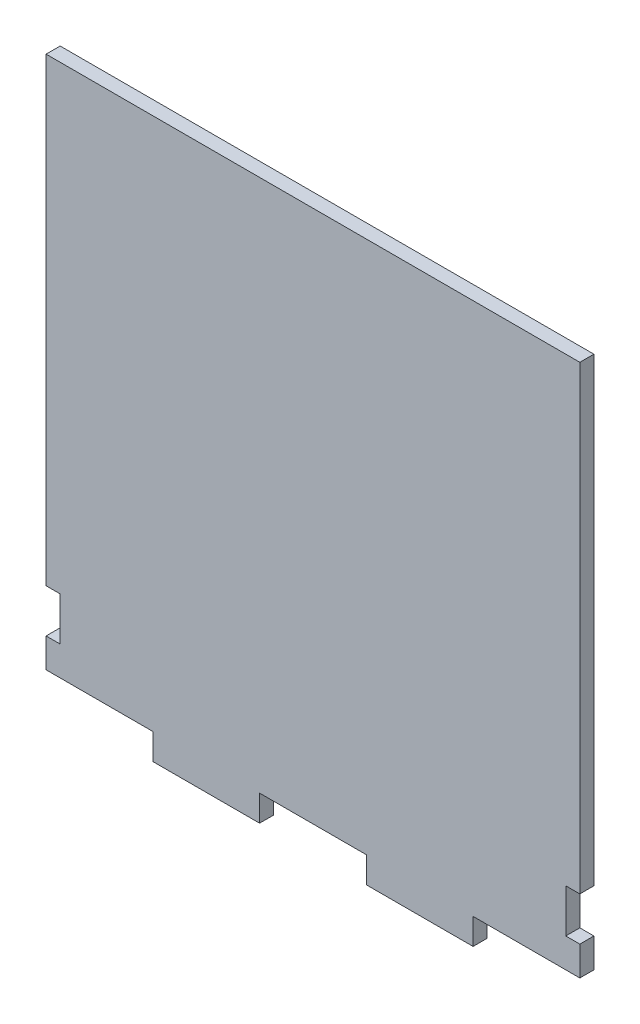
SolidWorks part; units mm, degrees
ref_plane "Ön Düzlem" through (0, 0, 0) normal (0, 0, 1) x (1, 0, 0)
ref_plane "Üst Düzlem" through (0, 0, 0) normal (0, 1, 0) x (1, 0, 0)
ref_plane "Sağ Düzlem" through (0, 0, 0) normal (1, 0, 0) x (0, 0, -1)
sketch "Sketch1" plane through (0, 0, 0) normal (0, 0, 1) x (1, 0, 0)
  line L4 (-51.2, -9.8) -> (-51.2, -4.1667)
  line L6 (51.2, -4.1667) -> (51.2, -9.8)
  line L9 (-30.72, -12.5) -> (-30.72, -9.8)
  line L10 (-51.2, -4.1667) -> (-48.5, -4.1667)
  line L11 (-51.2, 4.1667) -> (-48.5, 4.1667)
  line L16 (-10.24, -12.5) -> (-10.24, -9.8)
  line L17 (-48.5, 4.1667) -> (-48.5, -4.1667)
  line L18 (51.2, -9.8) -> (30.72, -9.8)
  line L19 (10.24, -12.5) -> (10.24, -9.8)
  line L20 (48.5, 4.1667) -> (48.5, -4.1667)
  line L21 (51.2, 4.1667) -> (48.5, 4.1667)
  line L22 (51.2, -4.1667) -> (48.5, -4.1667)
  line L25 (30.72, -12.5) -> (30.72, -9.8)
  line L26 (-30.72, -9.8) -> (-51.2, -9.8)
  line L27 (10.24, -9.8) -> (-10.24, -9.8)
  line L29 (-51.2, 92.5) -> (51.2, 92.5)
  line L31 (-51.2, 92.5) -> (-51.2, 4.1667)
  line L32 (51.2, 4.1667) -> (51.2, 92.5)
  line L33 (-30.72, -12.5) -> (-30.72, -14.8)
  line L34 (-30.72, -14.8) -> (-10.24, -14.8)
  line L35 (30.72, -14.8) -> (30.72, -12.5)
  line L36 (10.24, -12.5) -> (10.24, -14.8)
  line L37 (-10.24, -12.5) -> (-10.24, -14.8)
  line L38 (10.24, -14.8) -> (30.72, -14.8)
  point P0 (0, 0)
extrude "Boss-Extrude1" add sketch "Sketch1" along normal blind 2.7
